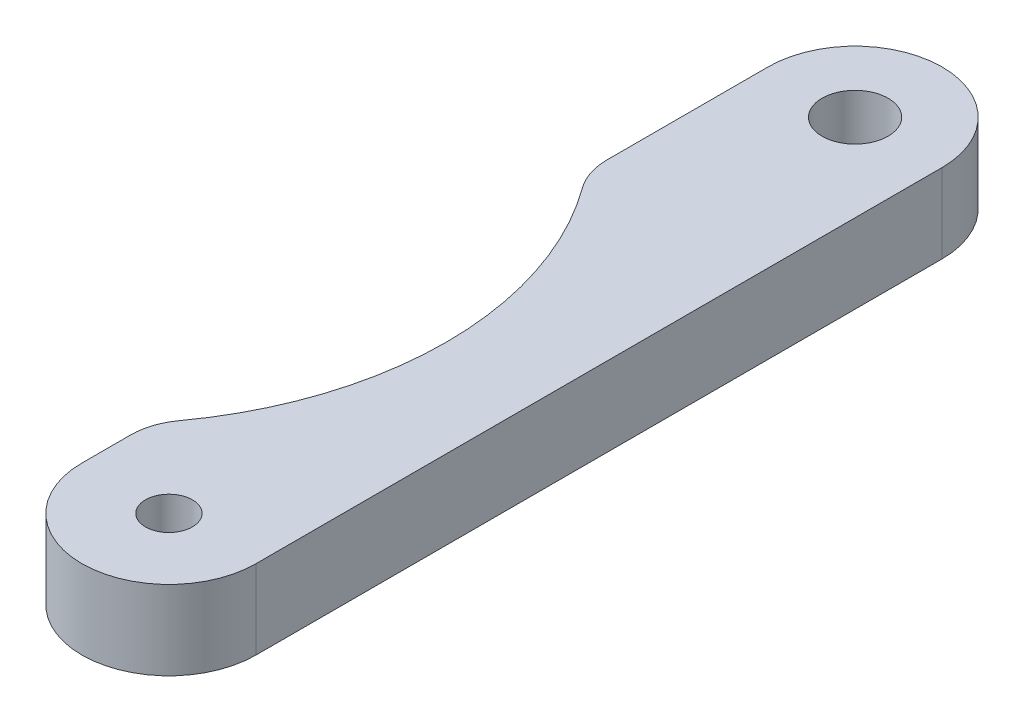
SolidWorks part; units mm, degrees
material "7075-T6, Plate (SS)"
ref_plane "Front Plane" through (0, 0, 0) normal (0, 0, 1) x (1, 0, 0)
ref_plane "Top Plane" through (0, 0, 0) normal (0, 1, 0) x (1, 0, 0)
ref_plane "Right Plane" through (0, 0, 0) normal (1, 0, 0) x (0, 0, -1)
sketch "Sketch1" plane through (0, 0, 0) normal (0, 1, 0) x (1, 0, 0)
  line L0 (0.3077, 6.5172) -> (0.3077, -26.5028)
  line L1 (8.6897, 6.5172) -> (8.6897, -26.5028)
  arc A0 (0.3077, 6.5172) -> (8.6897, 6.5172) centre (4.4987, 6.5172) cw
  arc A1 (8.6897, -26.5028) -> (0.3077, -26.5028) centre (4.4987, -26.5028) cw
  dimension "D1" = 33.02
  dimension "D2" = 8.382
extrude "Boss-Extrude1" add sketch "Sketch1" along normal blind 3.81
hole_wizard "#4-40 Tapped Hole1" positions "Sketch2" profile "Sketch3" tap size "#4-40" standard "ANSI Inch" end condition through all
sketch "Sketch2" plane through (0, 3.81, 0) normal (0, 1, 0) x (1, 0, 0)
  arc A0 (0.3077, -26.5028) -> (8.6897, -26.5028) centre (4.4987, -26.5028) ccw construction
  arc A1 (8.6897, 6.5172) -> (0.3077, 6.5172) centre (4.4987, 6.5172) ccw construction
  point P0 (4.4987, 6.5172)
  point P2 (4.4987, -26.5028)
sketch "Sketch3" plane through (4.4987, 3.81, -6.5172) normal (1, 0, 0) x (0, 0, 1)
  line L0 (0, 0) -> (0, 3.81)
  line L1 (0, 3.81) -> (1.1303, 3.81)
  line L2 (1.1303, 3.81) -> (1.1303, 0)
  line L5 (1.1303, 0) -> (0, 0)
  line L11 (0, -6.35) -> (0, 107.95) construction
  dimension "Thru Tap Drill Dia." = 2.2606
  dimension "Thru Tap Drill Depth" = 3.81
cosmetic thread "Hole Thread1" parameters "D2"=2.8448
sketch "Sketch4" plane through (0, 3.81, 0) normal (0, 1, 0) x (1, 0, 0)
  line L0 (0.3077, -17.1048) -> (-18.1923, -17.1048) construction
  line L1 (0.3077, 6.5172) -> (0.3077, -26.5028) construction
  circle A1 centre (4.4987, -26.5028) radius 1.1303 construction
  arc A5 (-22.8682, -25.473) -> (-2.034, 0.0929) centre (-12.4511, -12.69) ccw
  dimension "D1" = 16.49
  dimension "D2" = 9.398
  dimension "D3" = 18.5
extrude "Cut-Extrude1" cut sketch "Sketch4" against normal through all
sketch "Sketch5" plane through (0, 3.81, 0) normal (0, 1, 0) x (1, 0, 0)
  circle A0 centre (4.4987, 6.5172) radius 1.5875
extrude "Cut-Extrude2" cut sketch "Sketch5" against normal through all
fillet "Fillet1" radius 3 2 edges at (0.3077, 1.905, 23.1367) (0.3077, 1.905, 2.2433)
